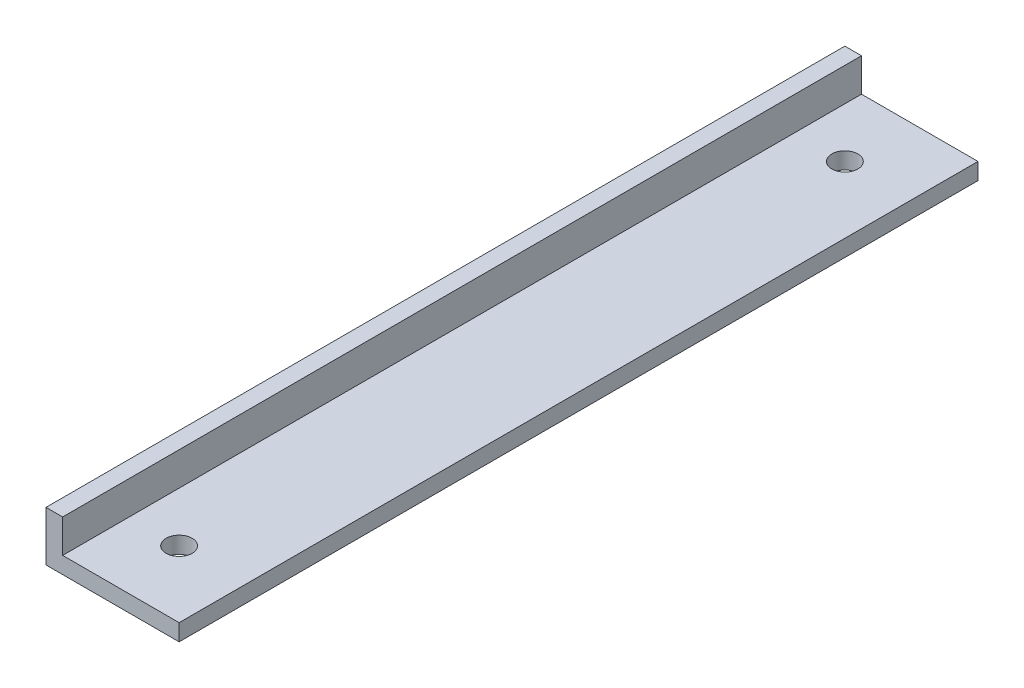
SolidWorks part; units mm, degrees
ref_plane "Front Plane" through (0, 0, 0) normal (0, 0, 1) x (1, 0, 0)
ref_plane "Top Plane" through (0, 0, 0) normal (0, 1, 0) x (1, 0, 0)
ref_plane "Right Plane" through (0, 0, 0) normal (1, 0, 0) x (0, 0, -1)
sketch "Sketch1" plane through (0, 0, 0) normal (0, 0, 1) x (1, 0, 0)
  line L0 (0, 0) -> (25.4, 0)
  line L1 (25.4, 0) -> (25.4, 3.175)
  line L2 (25.4, 3.175) -> (3.175, 3.175)
  line L3 (3.175, 3.175) -> (3.175, 25.4)
  line L4 (3.175, 25.4) -> (0, 25.4)
  line L5 (0, 25.4) -> (0, 0)
  line L6 (0, 9.525) -> (3.175, 9.525)
  dimension "D1" = 25.4
  dimension "D2" = 3.175
  dimension "D3" = 6.35
extrude "Boss-Extrude1" add sketch "Sketch1" along normal mid plane 152.4 contours L6 L5 L0 L1 L2 L3
sketch "Sketch2" plane through (0, 3.175, 0) normal (0, 1, 0) x (1, 0, 0)
  line L0 (25.4, 76.2) -> (3.175, 76.2) construction
  line L1 (25.4, -76.2) -> (3.175, -76.2) construction
  line L2 (25.4, -76.2) -> (25.4, 76.2) construction
  circle A1 centre (12.7, -63.5) radius 2.4892
  circle A2 centre (12.7, 63.5) radius 2.4892
  dimension "D1" = 4.9784
  dimension "D2" = 4.9784
  dimension "D3" = 12.7
  dimension "D4" = 12.7
  dimension "D5" = 12.7
  dimension "D6" = 12.7
extrude "Cut-Extrude1" cut sketch "Sketch2" against normal through all
